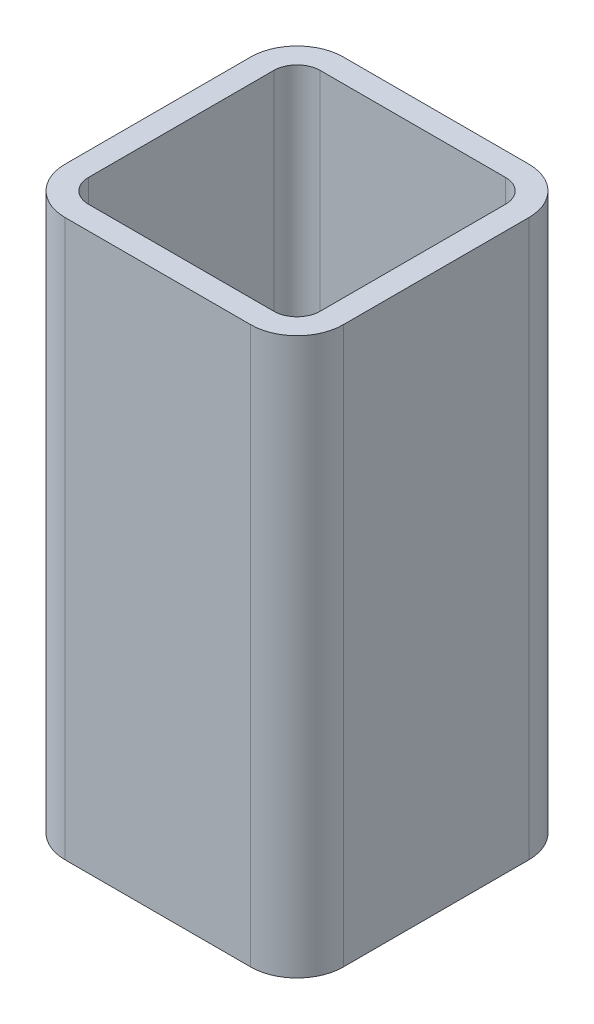
SolidWorks part; units mm, degrees
ref_plane "Front Plane" through (0, 0, 0) normal (0, 0, 1) x (1, 0, 0)
ref_plane "Top Plane" through (0, 0, 0) normal (0, 1, 0) x (1, 0, 0)
ref_plane "Right Plane" through (0, 0, 0) normal (1, 0, 0) x (0, 0, -1)
sketch "Sketch1" plane through (0, 0, 0) normal (0, 1, 0) x (1, 0, 0)
  line L0 (-50.8, -63.5) -> (50.8, -63.5)
  line L1 (-63.5, -50.8) -> (-63.5, 50.8)
  line L2 (50.8, 63.5) -> (-50.8, 63.5)
  line L3 (63.5, 50.8) -> (63.5, -50.8)
  line L4 (-50.8, -76.2) -> (50.8, -76.2)
  line L5 (-76.2, -50.8) -> (-76.2, 50.8)
  line L6 (50.8, 76.2) -> (-50.8, 76.2)
  line L7 (76.2, 50.8) -> (76.2, -50.8)
  arc A0 (76.2, 50.8) -> (50.8, 76.2) centre (50.8, 50.8) ccw
  arc A1 (50.8, -76.2) -> (76.2, -50.8) centre (50.8, -50.8) ccw
  arc A2 (-76.2, -50.8) -> (-50.8, -76.2) centre (-50.8, -50.8) ccw
  arc A3 (-50.8, 76.2) -> (-76.2, 50.8) centre (-50.8, 50.8) ccw
  arc A4 (-50.8, 63.5) -> (-63.5, 50.8) centre (-50.8, 50.8) ccw
  arc A5 (63.5, 50.8) -> (50.8, 63.5) centre (50.8, 50.8) ccw
  arc A6 (50.8, -63.5) -> (63.5, -50.8) centre (50.8, -50.8) ccw
  arc A7 (-63.5, -50.8) -> (-50.8, -63.5) centre (-50.8, -50.8) ccw
extrude "Boss-Extrude1" add sketch "Sketch1" along normal mid plane 304.8
